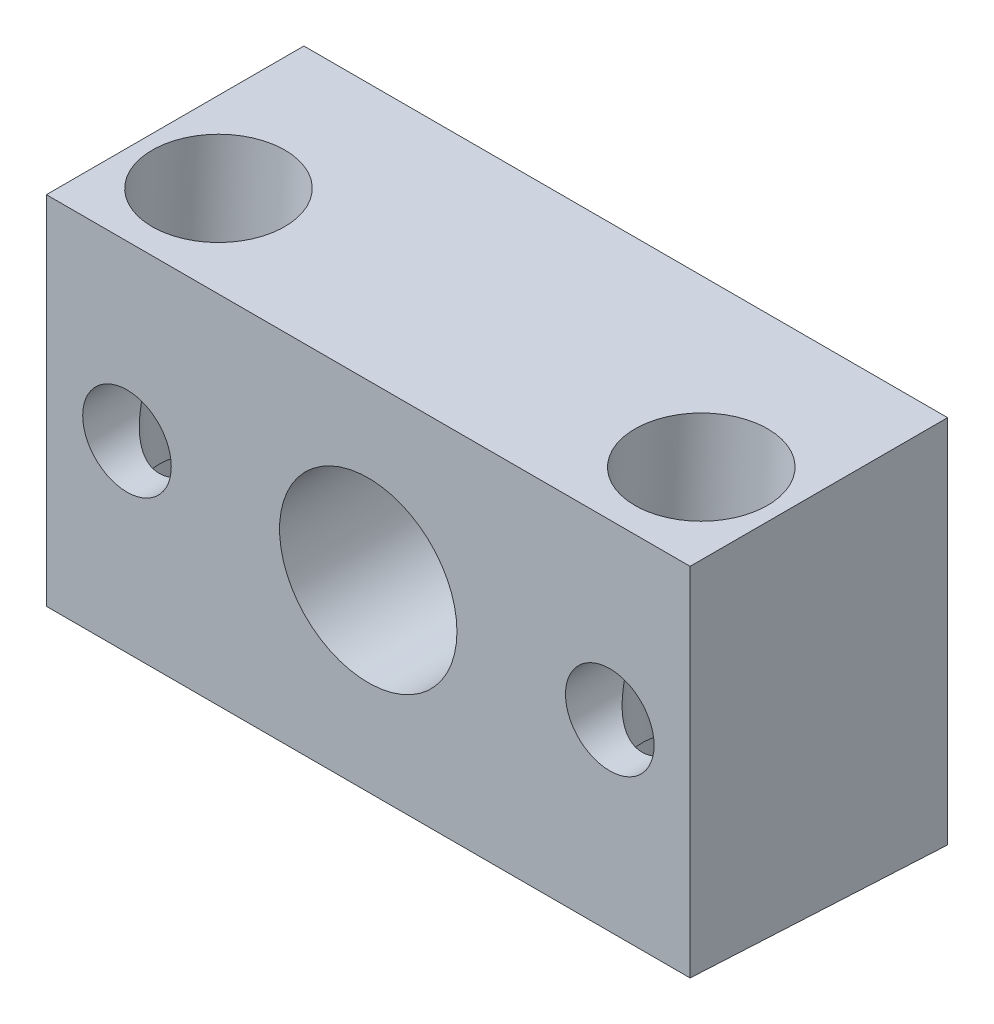
SolidWorks part; units mm, degrees
material "Alloy Steel"
ref_plane "Front Plane" through (0, 0, 0) normal (0, 0, 1) x (1, 0, 0)
ref_plane "Top Plane" through (0, 0, 0) normal (0, 1, 0) x (1, 0, 0)
ref_plane "Right Plane" through (0, 0, 0) normal (1, 0, 0) x (0, 0, -1)
sketch "Sketch1" plane through (0, 0, 0) normal (0, 0, 1) x (1, 0, 0)
  line L0 (0, 0) -> (0, 28.5118) construction
  line L1 (-31.75, 17.0688) -> (31.75, 17.0688)
  line L2 (-31.75, 17.0688) -> (-31.75, -19.431)
  line L3 (-31.75, -19.431) -> (31.75, -19.431)
  line L4 (31.75, 17.0688) -> (31.75, -19.431)
  circle A0 centre (0, 0) radius 8.7503
  circle A1 centre (-23.7998, 0) radius 4.3688
  circle A2 centre (23.8252, 0) radius 4.3688
  dimension "D4" = 17.5006
  dimension "D5" = 8.7376
  dimension "D1" = 63.5
  dimension "D2" = 36.4998
  dimension "D3" = 17.0688
  dimension "D6" = 23.7998
  dimension "D7" = 47.625
extrude "Extrude1" add sketch "Sketch1" along normal blind 25.4
sketch "Sketch2" plane through (31.75, 0, 0) normal (1, 0, 0) x (0, 0, -1)
  line L0 (0, -19.431) -> (-25.4, -18.0998)
  line L1 (-25.4, -19.431) -> (-25.4, 17.0688) construction
  line L2 (-25.4, -18.0998) -> (-25.4, -19.431)
  line L3 (-25.4, -19.431) -> (0, -19.431)
  dimension "D1" = 3
extrude "Cut-Extrude1" cut sketch "Sketch2" against normal through all
ref_plane "Plane1" through (-23.7998, 0, 0) normal (1, 0, 0) x (0, 0, -1)
sketch "Sketch3" plane through (-23.7998, 0, 0) normal (1, 0, 0) x (0, 0, -1)
  line L0 (-17.4498, 16.9318) -> (-17.4498, -17.6805) construction
  line L1 (-10.9093, -18.8593) -> (-10.9093, -8.3312)
  line L2 (0, -19.431) -> (-25.4, -18.0998) construction
  line L3 (-10.9093, -8.3312) -> (-12.6873, -8.3312)
  line L4 (-12.6873, -8.3312) -> (-12.6873, 17.0688)
  line L5 (0, -19.431) -> (0, 17.0688) construction
  line L6 (-25.4, 17.0688) -> (0, 17.0688) construction
  line L7 (-12.6873, 17.0688) -> (-17.4498, 17.0688)
  line L8 (-17.4498, 17.0688) -> (-17.4498, -18.8593)
  line L9 (-17.4498, -18.8593) -> (-10.9093, -18.8593)
  dimension "D1" = 17.4498
  dimension "D2" = 9.525
  dimension "D3" = 13.081
  dimension "D4" = 25.4
revolve "Cut-Revolve1" cut sketch "Sketch3" angle 360 about L0
sketch "Sketch4" plane through (-23.7998, 0, 0) normal (1, 0, 0) x (0, 0, -1)
  line L0 (-16.1471, 21.4133) -> (-17.2157, 1.0228) construction
  line L1 (0, -19.431) -> (-25.4, -18.0998) construction
  line L2 (-9.8253, 17.0688) -> (-10.3767, 6.5477)
  line L3 (-25.4, 17.0688) -> (0, 17.0688) construction
  line L4 (-10.3767, 6.5477) -> (-16.9082, 6.89)
  line L5 (-16.9082, 6.89) -> (-16.3568, 17.4111)
  line L6 (-16.3568, 17.4111) -> (-9.8253, 17.0688)
  dimension "D1" = 18.2626
  dimension "D2" = 25.4
  dimension "D3" = 13.081
revolve "Cut-Revolve2" cut sketch "Sketch4" angle 360 about L0
pattern_linear "LPattern1" count 2 spacing 47.625 along (1, 0, 0) of "Cut-Revolve1", "Cut-Revolve2"
